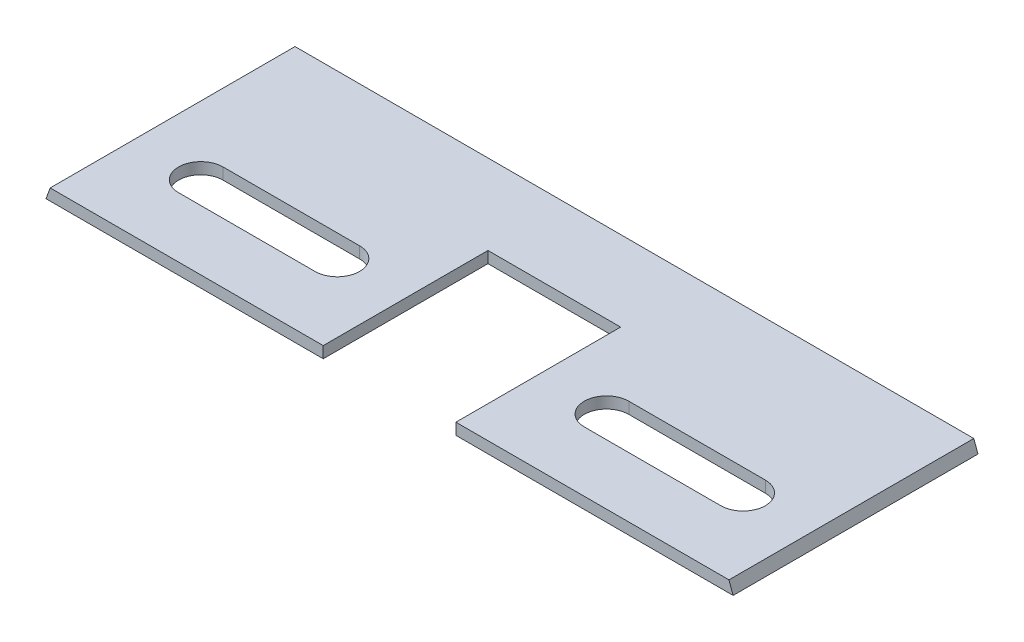
SolidWorks part; units mm, degrees
ref_plane "Front Plane" through (0, 0, 0) normal (0, 0, 1) x (1, 0, 0)
ref_plane "Top Plane" through (0, 0, 0) normal (0, 1, 0) x (1, 0, 0)
ref_plane "Right Plane" through (0, 0, 0) normal (1, 0, 0) x (0, 0, -1)
sketch "Sketch3" plane through (0, 0, 0) normal (0, 0, 1) x (1, 0, 0)
  line L0 (-76.2651, 1.199) -> (-77.169, -1.2845)
  line L1 (-77.169, -1.2845) -> (77.169, -1.2845)
  line L2 (77.169, -1.2845) -> (76.2651, 1.199)
  line L3 (-76.2651, 1.199) -> (-76.234, 1.2845)
  line L4 (-76.234, 1.2845) -> (76.0751, 1.2845)
  line L5 (76.2651, 1.199) -> (76.234, 1.2845)
  line L6 (76.234, 1.2845) -> (76.0751, 1.2845)
extrude "Boss-Extrude1" add sketch "Sketch3" against normal blind 55
sketch "Sketch4" plane through (0, 1.2845, 0) normal (0, 1, 0) x (1, 0, 0)
  line L0 (-14.9, 0) -> (-14.9, 37) construction
  line L1 (-14.9, 37) -> (14.9, 37) construction
  line L2 (14.9, 37) -> (14.9, 0.1154) construction
  line L3 (14.9, 0.1154) -> (79.5, 0.1154) construction
  line L4 (79.5, 0.1154) -> (79.5, 55) construction
  line L5 (79.5, 55) -> (-79.5, 55) construction
  line L6 (-79.5, 55) -> (-79.5, 0) construction
  line L7 (-79.5, 0) -> (-14.9, 0) construction
  line L8 (-14.9, 0) -> (-14.9, 37)
  line L9 (-14.9, 37) -> (14.9, 37)
  line L10 (14.9, 37) -> (14.9, 0.1154)
  line L12 (-14.9, 0) -> (-14.9, -2.5147)
  line L13 (-14.9, -2.5147) -> (14.9, -2.5147)
  line L14 (14.9, -2.5147) -> (14.9, 0.1154)
  point P9 (0, 37)
extrude "Cut-Extrude4" cut sketch "Sketch4" against normal blind 3
sketch "Sketch5" plane through (0, 1.2845, 0) normal (0, 1, 0) x (1, 0, 0)
  line L0 (0, 0) -> (0, 55) construction
  line L1 (76.234, 55) -> (-76.234, 55) construction
  line L3 (-14.9, 37) -> (-14.9, 0) construction
  line L4 (-76.234, 55) -> (-76.234, 0) construction
  line L5 (14.9, 18.5) -> (76.234, 18.5) construction
  line L6 (14.9, 0) -> (14.9, 37) construction
  line L7 (76.234, 55) -> (76.234, 0) construction
  line L8 (-45.567, 18.5) -> (-45.567, 0) construction
  line L9 (-14.9, 0) -> (-76.234, 0) construction
  line L10 (45.567, 18.5) -> (45.567, 0) construction
  line L11 (76.234, 0) -> (14.9, 0) construction
  line L12 (-45.567, 18.5) -> (-45.567, 55) construction
  line L13 (45.567, 18.5) -> (45.567, 55) construction
  line L14 (-45.567, 18.5) -> (-76.234, 18.5) construction
  line L15 (-45.567, 18.5) -> (-14.9, 18.5) construction
  line L16 (-60.9005, 23.5) -> (-30.2335, 23.5)
  line L17 (-60.9005, 13.5) -> (-30.2335, 13.5)
  line L18 (60.9005, 13.5) -> (30.2335, 13.5)
  line L19 (60.9005, 23.5) -> (30.2335, 23.5)
  arc A1 (-60.9005, 23.5) -> (-60.9005, 13.5) centre (-60.9005, 18.5) ccw
  arc A2 (-30.2335, 13.5) -> (-30.2335, 23.5) centre (-30.2335, 18.5) ccw
  arc A3 (30.2335, 13.5) -> (30.2335, 23.5) centre (30.2335, 18.5) cw
  arc A4 (60.9005, 23.5) -> (60.9005, 13.5) centre (60.9005, 18.5) cw
  dimension "D1" = 10
  dimension "D2" = 10
extrude "Cut-Extrude5" cut sketch "Sketch5" against normal blind 3
